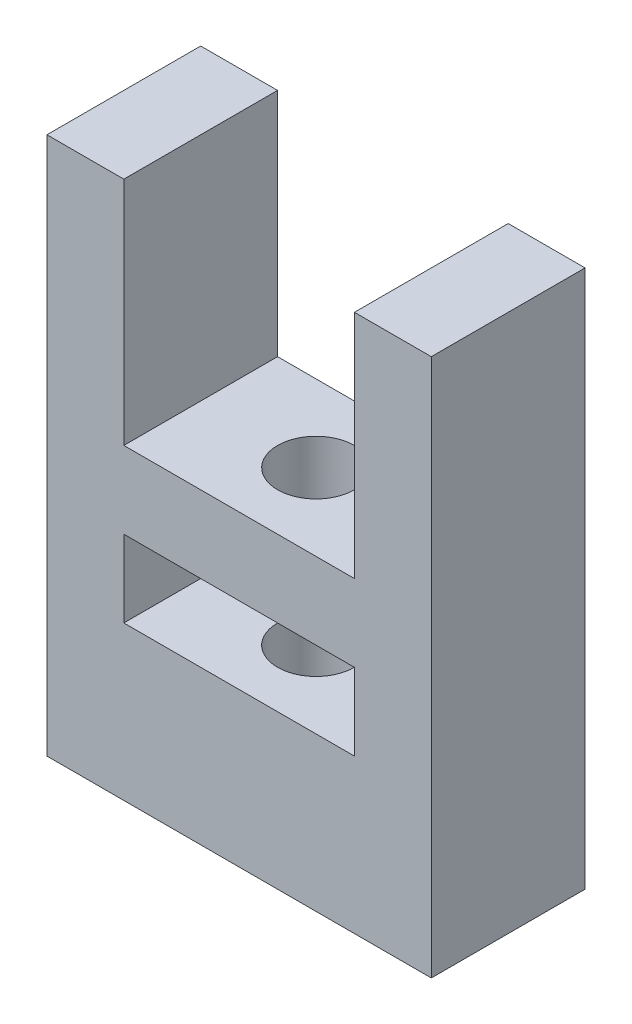
SolidWorks part; units mm, degrees
ref_plane "Plano frontal" through (0, 0, 0) normal (0, 0, 1) x (1, 0, 0)
ref_plane "Plano superior" through (0, 0, 0) normal (0, 1, 0) x (1, 0, 0)
ref_plane "Plano direito" through (0, 0, 0) normal (1, 0, 0) x (0, 0, -1)
sketch "Esboço1" plane through (0, 0, 0) normal (0, 0, 1) x (1, 0, 0)
  line L0 (-40, 70) -> (-50, 70)
  line L1 (0, 0) -> (-50, 0)
  line L2 (0, 0) -> (0, 70)
  line L3 (0, 70) -> (-10, 70)
  line L4 (-50, 0) -> (-50, 70)
  line L6 (-40, 70) -> (-40, 40)
  line L7 (-40, 40) -> (-10, 40)
  line L8 (-10, 70) -> (-10, 40)
  line L9 (-40, 30) -> (-10, 30)
  line L10 (-40, 30) -> (-40, 20)
  line L11 (-40, 20) -> (-10, 20)
  line L12 (-10, 30) -> (-10, 20)
  dimension "D1" = 50
  dimension "D2" = 70
  dimension "D3" = 30
  dimension "D4" = 30
  dimension "D5" = 10
  dimension "D6" = 30
  dimension "D7" = 20
  dimension "D8" = 10
extrude "Ressalto-extrusão1" add sketch "Esboço1" along normal blind 20
sketch "Esboço2" plane through (0, 40, 0) normal (0, 1, 0) x (1, 0, 0)
  line L0 (-25, -20) -> (-25, 0) construction
  line L1 (-10, -20) -> (-40, -20) construction
  line L2 (-10, 0) -> (-40, 0) construction
  circle A0 centre (-25, -10) radius 5
  dimension "D1" = 10
extrude "Corte-extrusão1" cut sketch "Esboço2" against normal through all
